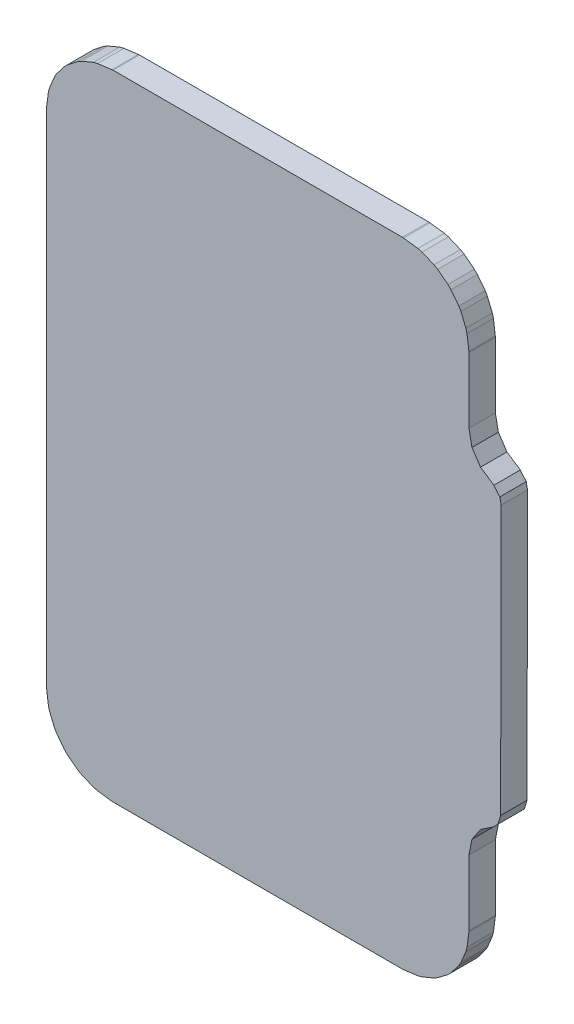
SolidWorks part; units mm, degrees
ref_plane "Front Plane" through (0, 0, 0) normal (0, 0, 1) x (1, 0, 0)
ref_plane "Top Plane" through (0, 0, 0) normal (0, 1, 0) x (1, 0, 0)
ref_plane "Right Plane" through (0, 0, 0) normal (1, 0, 0) x (0, 0, -1)
sketch "Model" plane through (0, 0, 0) normal (0, 0, 1) x (1, 0, 0)
  line L0 (-0.7397, 1.382) -> (-0.6305, 1.368)
  line L1 (-0.6305, 1.368) -> (-0.5992, 1.36)
  line L2 (-0.5992, 1.36) -> (-0.5088, 1.322)
  line L3 (-0.5088, 1.322) -> (-0.4808, 1.306)
  line L4 (-0.4808, 1.306) -> (-0.4031, 1.246)
  line L5 (-0.4031, 1.246) -> (-0.3802, 1.223)
  line L6 (-0.3802, 1.223) -> (-0.3206, 1.146)
  line L7 (-0.3206, 1.146) -> (-0.3045, 1.118)
  line L8 (-0.3045, 1.118) -> (-0.267, 1.027)
  line L9 (-0.267, 1.027) -> (-0.2586, 0.996)
  line L10 (-0.2586, 0.996) -> (-0.2442, 0.887)
  line L11 (-0.2442, 0.887) -> (-0.2437, 0.879)
  line L12 (-0.2437, 0.879) -> (-0.2437, 0.383)
  line L13 (-0.2437, 0.383) -> (-0.2209, 0.268)
  line L14 (-0.2209, 0.268) -> (-0.156, 0.171)
  line L15 (-0.156, 0.171) -> (-0.055, 0.103)
  line L16 (-0.055, 0.103) -> (-0.01, 0.049)
  line L17 (-0.01, 0.049) -> (0, 0)
  line L18 (0, 0) -> (-0.004, -2.038)
  line L19 (-0.004, -2.038) -> (-0.024, -2.105)
  line L20 (-0.024, -2.105) -> (-0.06, -2.141)
  line L21 (-0.06, -2.141) -> (-0.156, -2.205)
  line L22 (-0.156, -2.205) -> (-0.2209, -2.302)
  line L23 (-0.2209, -2.302) -> (-0.2437, -2.417)
  line L24 (-0.2437, -2.417) -> (-0.2437, -2.913)
  line L25 (-0.2437, -2.913) -> (-0.2442, -2.921)
  line L26 (-0.2442, -2.921) -> (-0.2586, -3.03)
  line L27 (-0.2586, -3.03) -> (-0.267, -3.062)
  line L28 (-0.267, -3.062) -> (-0.3044, -3.152)
  line L29 (-0.3044, -3.152) -> (-0.3206, -3.18)
  line L30 (-0.3206, -3.18) -> (-0.3802, -3.258)
  line L31 (-0.3802, -3.258) -> (-0.4031, -3.281)
  line L32 (-0.4031, -3.281) -> (-0.4807, -3.34)
  line L33 (-0.4807, -3.34) -> (-0.5088, -3.356)
  line L34 (-0.5088, -3.356) -> (-0.5992, -3.394)
  line L35 (-0.5992, -3.394) -> (-0.6305, -3.402)
  line L36 (-0.6305, -3.402) -> (-0.7397, -3.417)
  line L37 (-0.7397, -3.417) -> (-0.7478, -3.417)
  line L38 (-0.7478, -3.417) -> (-2.9396, -3.417)
  line L39 (-2.9396, -3.417) -> (-2.9477, -3.417)
  line L40 (-2.9477, -3.417) -> (-3.0569, -3.402)
  line L41 (-3.0569, -3.402) -> (-3.0882, -3.394)
  line L42 (-3.0882, -3.394) -> (-3.1786, -3.356)
  line L43 (-3.1786, -3.356) -> (-3.2067, -3.34)
  line L44 (-3.2067, -3.34) -> (-3.2843, -3.281)
  line L45 (-3.2843, -3.281) -> (-3.3072, -3.258)
  line L46 (-3.3072, -3.258) -> (-3.3668, -3.18)
  line L47 (-3.3668, -3.18) -> (-3.383, -3.152)
  line L48 (-3.383, -3.152) -> (-3.4204, -3.062)
  line L49 (-3.4204, -3.062) -> (-3.4288, -3.03)
  line L50 (-3.4288, -3.03) -> (-3.4432, -2.921)
  line L51 (-3.4432, -2.921) -> (-3.4437, -2.913)
  line L52 (-3.4437, -2.913) -> (-3.4437, 0.879)
  line L53 (-3.4437, 0.879) -> (-3.4432, 0.887)
  line L54 (-3.4432, 0.887) -> (-3.4288, 0.996)
  line L55 (-3.4288, 0.996) -> (-3.4204, 1.027)
  line L56 (-3.4204, 1.027) -> (-3.3829, 1.118)
  line L57 (-3.3829, 1.118) -> (-3.3668, 1.146)
  line L58 (-3.3668, 1.146) -> (-3.3072, 1.223)
  line L59 (-3.3072, 1.223) -> (-3.2843, 1.246)
  line L60 (-3.2843, 1.246) -> (-3.2066, 1.306)
  line L61 (-3.2066, 1.306) -> (-3.1786, 1.322)
  line L62 (-3.1786, 1.322) -> (-3.0882, 1.36)
  line L63 (-3.0882, 1.36) -> (-3.0569, 1.368)
  line L64 (-3.0569, 1.368) -> (-2.9477, 1.382)
  line L65 (-2.9477, 1.382) -> (-2.9396, 1.383)
  line L66 (-2.9396, 1.383) -> (-0.7478, 1.383)
  line L67 (-0.7478, 1.383) -> (-0.7397, 1.382)
  line L68 (25.081, 4.408) -> (25.127, 4.355)
  line L69 (25.127, 4.355) -> (25.138, 4.304)
  line L70 (25.138, 4.304) -> (25.138, 3.44)
  line L71 (25.138, 3.44) -> (25.136, 3.416)
  line L72 (25.136, 3.416) -> (25.128, 3.375)
  line L73 (25.128, 3.375) -> (25.109, 3.331)
  line L74 (25.109, 3.331) -> (25.093, 3.307)
  line L75 (25.093, 3.307) -> (25.059, 3.273)
  line L76 (25.059, 3.273) -> (25.035, 3.257)
  line L77 (25.035, 3.257) -> (24.99, 3.238)
  line L78 (24.99, 3.238) -> (24.95, 3.23)
  line L79 (24.95, 3.23) -> (24.926, 3.228)
  line L80 (24.926, 3.228) -> (23.85, 3.228)
  line L81 (23.85, 3.228) -> (23.826, 3.23)
  line L82 (23.826, 3.23) -> (23.786, 3.238)
  line L83 (23.786, 3.238) -> (23.741, 3.257)
  line L84 (23.741, 3.257) -> (23.717, 3.273)
  line L85 (23.717, 3.273) -> (23.683, 3.307)
  line L86 (23.683, 3.307) -> (23.667, 3.331)
  line L87 (23.667, 3.331) -> (23.648, 3.375)
  line L88 (23.648, 3.375) -> (23.64, 3.416)
  line L89 (23.64, 3.416) -> (23.638, 3.44)
  line L90 (23.638, 3.44) -> (23.638, 4.304)
  line L91 (23.638, 4.304) -> (23.658, 4.371)
  line L92 (23.658, 4.371) -> (23.711, 4.416)
  line L93 (23.711, 4.416) -> (23.762, 4.428)
  line L94 (23.762, 4.428) -> (25.014, 4.428)
  line L95 (25.014, 4.428) -> (25.081, 4.408)
extrude "Boss-Extrude1" add sketch "Model" along normal blind 0.2
delete or keep bodies "Body-Delete/Keep 1" type delete bodies bodies 102
